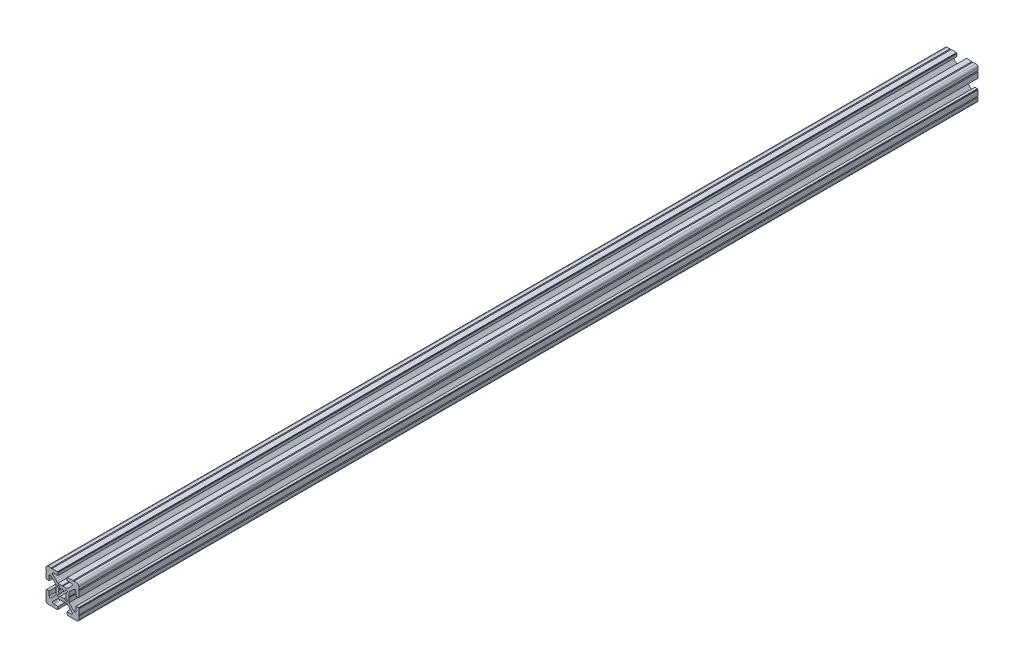
SolidWorks part; units mm, degrees
ref_plane "Front Plane" through (0, 0, 0) normal (0, 0, 1) x (1, 0, 0)
ref_plane "Top Plane" through (0, 0, 0) normal (0, 1, 0) x (1, 0, 0)
ref_plane "Right Plane" through (0, 0, 0) normal (1, 0, 0) x (0, 0, -1)
ref_plane "Plane1" through (0, 0, -720) normal (0, 0, -1) x (-1, 0, 0)
sketch "Sketch1" plane through (0, 0, -720) normal (0, 0, -1) x (-1, 0, 0)
  line L0 (4.8083, 3.677) -> (2.9023, 1.771)
  line L1 (2.9023, -1.771) -> (4.8083, -3.677)
  line L2 (4.8083, -3.677) -> (3.677, -4.8083)
  line L3 (3.677, -4.8083) -> (1.771, -2.9023)
  line L4 (-1.771, -2.9023) -> (-3.677, -4.8083)
  line L5 (-3.677, -4.8083) -> (-4.8083, -3.677)
  line L6 (-4.8083, -3.677) -> (-2.9023, -1.771)
  line L7 (-2.9023, 1.771) -> (-4.8083, 3.677)
  line L8 (-4.8083, 3.677) -> (-3.677, 4.8083)
  line L9 (-3.677, 4.8083) -> (-1.771, 2.9023)
  line L10 (1.771, 2.9023) -> (3.677, 4.8083)
  line L11 (3.677, 4.8083) -> (4.8083, 3.677)
  line L12 (-15, 13) -> (-15, 10.5)
  line L13 (-15, 10.5) -> (-14.5, 10)
  line L14 (-14.5, 10) -> (-15, 9.5)
  line L15 (-15, 9.5) -> (-15, 4.5)
  line L16 (-15, 4.5) -> (-14.5, 4.5)
  line L17 (-14.5, 4.5) -> (-14.5, 4)
  line L18 (-14.5, 4) -> (-12.2, 4)
  line L19 (-12.2, 4) -> (-12.2, 8)
  line L20 (-10.4929, 8.7071) -> (-6, 4.2142)
  line L21 (-6, 4.2142) -> (-6, 0.3125)
  line L22 (-6, 0.3125) -> (-5.7, 0)
  line L23 (-5.7, 0) -> (-6, -0.3125)
  line L24 (-6, -0.3125) -> (-6, -4.2142)
  line L25 (-6, -4.2142) -> (-10.4929, -8.7071)
  line L26 (-12.2, -8) -> (-12.2, -4)
  line L27 (-12.2, -4) -> (-14.5, -4)
  line L28 (-14.5, -4) -> (-14.5, -4.5)
  line L29 (-14.5, -4.5) -> (-15, -4.5)
  line L30 (-15, -4.5) -> (-15, -9.5)
  line L31 (-15, -9.5) -> (-14.5, -10)
  line L32 (-14.5, -10) -> (-15, -10.5)
  line L33 (-15, -10.5) -> (-15, -13)
  line L34 (-13, -15) -> (-10.5, -15)
  line L35 (-10.5, -15) -> (-10, -14.5)
  line L36 (-10, -14.5) -> (-9.5, -15)
  line L37 (-9.5, -15) -> (-4.5, -15)
  line L38 (-4.5, -15) -> (-4.5, -14.5)
  line L39 (-4.5, -14.5) -> (-4, -14.5)
  line L40 (-4, -14.5) -> (-4, -12.2)
  line L41 (-4, -12.2) -> (-8, -12.2)
  line L42 (-8.7071, -10.4929) -> (-4.2142, -6)
  line L43 (-4.2142, -6) -> (-0.3125, -6)
  line L44 (-0.3125, -6) -> (0, -5.7)
  line L45 (0, -5.7) -> (0.3125, -6)
  line L46 (0.3125, -6) -> (4.2142, -6)
  line L47 (4.2142, -6) -> (8.7071, -10.4929)
  line L48 (8, -12.2) -> (4, -12.2)
  line L49 (4, -12.2) -> (4, -14.5)
  line L50 (4, -14.5) -> (4.5, -14.5)
  line L51 (4.5, -14.5) -> (4.5, -15)
  line L52 (4.5, -15) -> (9.5, -15)
  line L53 (9.5, -15) -> (9.9899, -14.5)
  line L54 (9.9899, -14.5) -> (10.4899, -15)
  line L55 (10.4899, -15) -> (13, -15)
  line L56 (15, -13) -> (15, -10.5)
  line L57 (15, -10.5) -> (14.5, -10)
  line L58 (14.5, -10) -> (15, -9.5)
  line L59 (15, -9.5) -> (15, -4.5)
  line L60 (15, -4.5) -> (14.5, -4.5)
  line L61 (14.5, -4.5) -> (14.5, -4)
  line L62 (14.5, -4) -> (12.2, -4)
  line L63 (12.2, -4) -> (12.2, -8)
  line L64 (10.4929, -8.7071) -> (6, -4.2142)
  line L65 (6, -4.2142) -> (6, -0.3125)
  line L66 (6, -0.3125) -> (5.7, 0)
  line L67 (5.7, 0) -> (6, 0.3125)
  line L68 (6, 0.3125) -> (6, 4.2142)
  line L69 (6, 4.2142) -> (10.4929, 8.7071)
  line L70 (12.2, 8) -> (12.2, 4)
  line L71 (12.2, 4) -> (14.5, 4)
  line L72 (14.5, 4) -> (14.5, 4.5)
  line L73 (14.5, 4.5) -> (15, 4.5)
  line L74 (15, 4.5) -> (15, 9.5)
  line L75 (15, 9.5) -> (14.5, 10)
  line L76 (14.5, 10) -> (15, 10.5)
  line L77 (15, 10.5) -> (15, 13)
  line L78 (13, 15) -> (10.5, 15)
  line L79 (10.5, 15) -> (10, 14.5)
  line L80 (10, 14.5) -> (9.5, 15)
  line L81 (9.5, 15) -> (4.5, 15)
  line L82 (4.5, 15) -> (4.5, 14.5)
  line L83 (4.5, 14.5) -> (4, 14.5)
  line L84 (4, 14.5) -> (4, 12.2)
  line L85 (4, 12.2) -> (8, 12.2)
  line L86 (8.7071, 10.4929) -> (4.2142, 6)
  line L87 (4.2142, 6) -> (0.3125, 6)
  line L88 (0.3125, 6) -> (0, 5.7)
  line L89 (0, 5.7) -> (-0.3125, 6)
  line L90 (-0.3125, 6) -> (-4.2142, 6)
  line L91 (-4.2142, 6) -> (-8.7071, 10.4929)
  line L92 (-8, 12.2) -> (-4, 12.2)
  line L93 (-4, 12.2) -> (-4, 14.5)
  line L94 (-4, 14.5) -> (-4.5, 14.5)
  line L95 (-4.5, 14.5) -> (-4.5, 15)
  line L96 (-4.5, 15) -> (-9.5, 15)
  line L97 (-9.5, 15) -> (-10, 14.5)
  line L98 (-10, 14.5) -> (-10.5, 15)
  line L99 (-10.5, 15) -> (-13, 15)
  arc A0 (2.9023, 1.771) -> (2.9023, -1.771) centre (0, 0) cw
  arc A1 (1.771, -2.9023) -> (-1.771, -2.9023) centre (0, 0) cw
  arc A2 (-2.9023, -1.771) -> (-2.9023, 1.771) centre (0, 0) cw
  arc A3 (-1.771, 2.9023) -> (1.771, 2.9023) centre (0, 0) cw
  arc A4 (-13, 15) -> (-15, 13) centre (-13, 13) ccw
  arc A5 (-12.2, 8) -> (-10.4929, 8.7071) centre (-11.2, 8) cw
  arc A6 (-10.4929, -8.7071) -> (-12.2, -8) centre (-11.2, -8) cw
  arc A7 (-15, -13) -> (-13, -15) centre (-13, -13) ccw
  arc A8 (-8, -12.2) -> (-8.7071, -10.4929) centre (-8, -11.2) cw
  arc A9 (8.7071, -10.4929) -> (8, -12.2) centre (8, -11.2) cw
  arc A10 (13, -15) -> (15, -13) centre (13, -13) ccw
  arc A11 (12.2, -8) -> (10.4929, -8.7071) centre (11.2, -8) cw
  arc A12 (10.4929, 8.7071) -> (12.2, 8) centre (11.2, 8) cw
  arc A13 (15, 13) -> (13, 15) centre (13, 13) ccw
  arc A14 (8, 12.2) -> (8.7071, 10.4929) centre (8, 11.2) cw
  arc A15 (-8.7071, 10.4929) -> (-8, 12.2) centre (-8, 11.2) cw
extrude "Boss-Extrude1" add sketch "Sketch1" against normal blind 820
ref_plane "Plane2" through (0, 0, -310) normal (0, 0, -1) x (-1, 0, 0)
